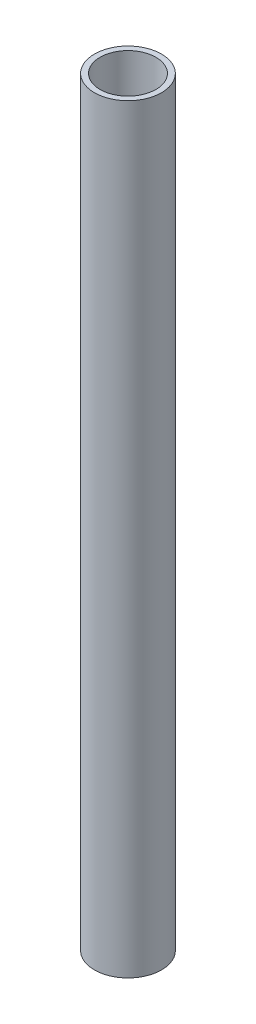
SolidWorks part; units mm, degrees
material "6061 Alloy"
ref_plane "Front Plane" through (0, 0, 0) normal (0, 0, 1) x (1, 0, 0)
ref_plane "Top Plane" through (0, 0, 0) normal (0, 1, 0) x (1, 0, 0)
ref_plane "Right Plane" through (0, 0, 0) normal (1, 0, 0) x (0, 0, -1)
sketch "Sketch2" plane through (0, 0, 0) normal (0, 1, 0) x (1, 0, 0)
  circle A0 centre (0, 0) radius 19.05
  circle A1 centre (0, 0) radius 15.875
  dimension "D1" = 38.1
  dimension "D2" = 3.175
extrude "Boss-Extrude1" add sketch "Sketch2" along normal blind 431.8
